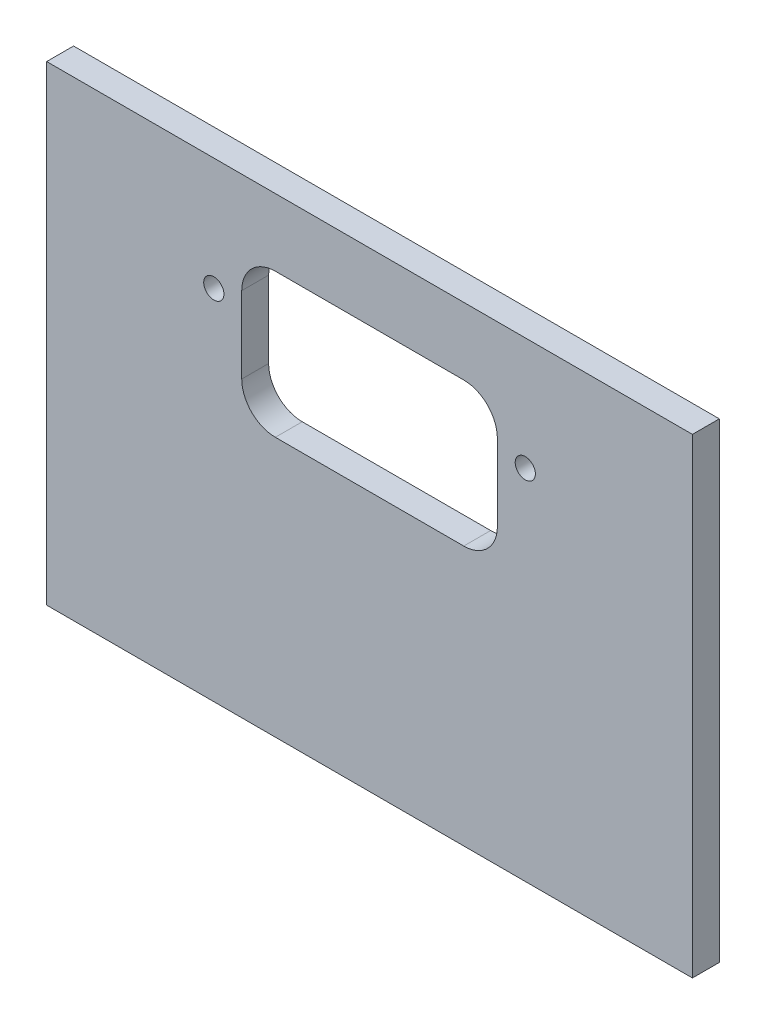
SolidWorks part; units mm, degrees
material "7075-T6 (SN)"
ref_plane "Plano frontal" through (0, 0, 0) normal (0, 0, 1) x (1, 0, 0)
ref_plane "Plano superior" through (0, 0, 0) normal (0, 1, 0) x (1, 0, 0)
ref_plane "Plano direito" through (0, 0, 0) normal (1, 0, 0) x (0, 0, -1)
sketch "Esboço1" plane through (0, 0, 0) normal (0, 0, 1) x (1, 0, 0)
  line L1 (0, 0) -> (96.01, 0)
  line L2 (0, 0) -> (0, -70)
  line L3 (0, -70) -> (96.01, -70)
  line L4 (96.01, 0) -> (96.01, -70)
  dimension "D1" = 70
  dimension "D2" = 96.01
extrude "Ressalto-extrusão1" add sketch "Esboço1" along normal blind 4
sketch "Esboço2" plane through (0, -70, 0) normal (0, -1, 0) x (-1, 0, 0)
  line L0 (0, -2) -> (-96.01, -2) construction
  line L1 (0, -4) -> (0, 0) construction
  line L2 (-96.01, -4) -> (-96.01, 0) construction
  circle A0 centre (-48.005, -2) radius 1.25
  circle A1 centre (-10, -2) radius 1.25
  circle A2 centre (-30, -2) radius 1.25
  circle A3 centre (-66.01, -2) radius 1.25
  circle A4 centre (-86.01, -2) radius 1.25
  dimension "D1" = 2.5
  dimension "D2" = 2.5
  dimension "D3" = 2.5
  dimension "D4" = 2.5
  dimension "D5" = 2.5
  dimension "D6" = 10
  dimension "D7" = 20
  dimension "D8" = 10
  dimension "D9" = 20
extrude "Corte-extrusão1" cut sketch "Esboço2" against normal blind 12
sketch "Esboço3" plane through (0, 0, 4) normal (0, 0, 1) x (1, 0, 0)
  line L0 (0, 0) -> (0, -70) construction
  line L1 (29, -10) -> (67.01, -10)
  line L2 (29, -10) -> (29, -31.382)
  line L3 (29, -31.382) -> (67.01, -31.382)
  line L4 (67.01, -10) -> (67.01, -31.382)
  line L5 (96.01, -70) -> (96.01, 0) construction
  line L6 (96.01, 0) -> (0, 0) construction
  line L7 (71.16, -16.78) -> (96.01, -16.78) construction
  line L8 (24.85, -16.78) -> (0, -16.78) construction
  line L9 (24.85, -16.78) -> (24.85, 0) construction
  line L10 (71.16, -16.78) -> (71.16, 0) construction
  circle A0 centre (24.85, -16.78) radius 1.5
  circle A1 centre (71.16, -16.78) radius 1.5
  dimension "D6" = 3
  dimension "D7" = 3
  dimension "D1" = 29
  dimension "D2" = 29
  dimension "D3" = 10
  dimension "D4" = 24.85
  dimension "D5" = 24.85
  dimension "D8" = 16.78
  dimension "D9" = 16.78
extrude "Corte-extrusão2" cut sketch "Esboço3" against normal blind 10
fillet "Filete1" radius 5 4 edges at (29, -31.382, 2) (29, -10, 2) (67.01, -31.382, 2) (67.01, -10, 2)
